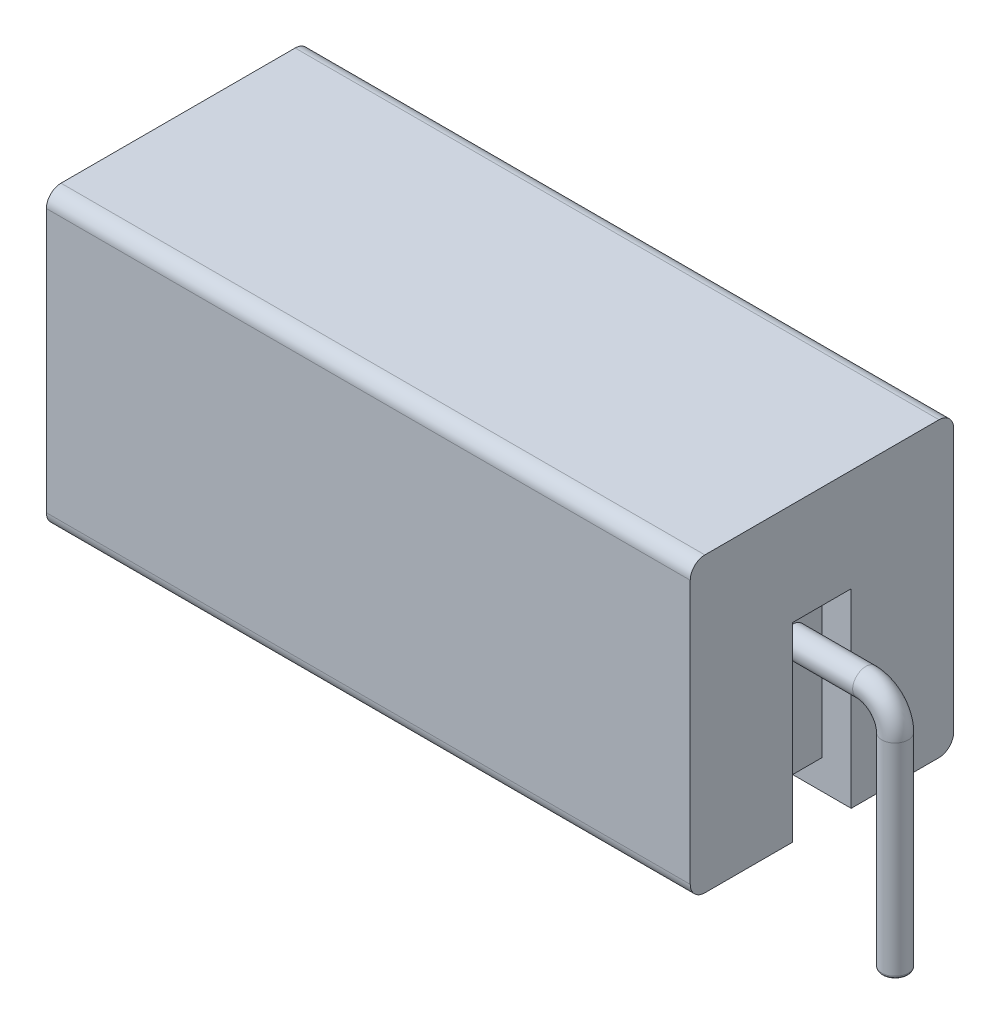
SolidWorks part; units mm, degrees
ref_plane "Front Plane" through (0, 0, 0) normal (0, 0, 1) x (1, 0, 0)
ref_plane "Top Plane" through (0, 0, 0) normal (0, 1, 0) x (1, 0, 0)
ref_plane "Right Plane" through (0, 0, 0) normal (1, 0, 0) x (0, 0, -1)
sketch "Sketch1" plane through (0, 0, 0) normal (0, 0, 1) x (1, 0, 0)
  line L1 (0, 0) -> (22, 0)
  line L2 (0, 0) -> (0, -10)
  line L3 (0, -10) -> (22, -10)
  line L4 (22, 0) -> (22, -10)
  dimension "D1" = 22
  dimension "D2" = 10
extrude "Boss-Extrude1" add sketch "Sketch1" along normal blind 9 contours L1 L4 L3 L2
fillet "Fillet2" radius 0.5 4 edges at (11, 0, 0) (11, -10, 0) (11, -10, 9) (11, 0, 9)
sketch3d "3DSketch1"
  line L1 (22, -10, 8.5) -> (22, -10, 0.5) construction
  line L3 (22, -10, 5.5) -> (22, -3.5, 5.5)
  line L4 (22, -3.5, 5.5) -> (22, -3.5, 3.5)
  line L5 (22, -3.5, 3.5) -> (22, -10, 3.5)
  line L7 (22, -10, 5.5) -> (22, -10, 3.5)
  dimension "D1" = 2
  dimension "D2" = 6.5
sketch "Sketch6" plane through (0, -10, 0) normal (0, -1, 0) x (1, 0, 0)
  line L5 (1, 5.5) -> (1, 3.5)
  line L6 (21, 5.5) -> (21, 3.5)
  line L8 (3, 8) -> (19, 8)
  line L10 (19, 1) -> (3, 1)
  line L13 (3, 8) -> (3, 5.5)
  line L14 (3, 1) -> (3, 3.5)
  line L15 (19, 8) -> (19, 5.5)
  line L16 (19, 1) -> (19, 3.5)
  line L17 (1, 5.5) -> (3, 5.5)
  line L18 (19, 5.5) -> (21, 5.5)
  line L19 (21, 3.5) -> (19, 3.5)
  line L20 (1, 3.5) -> (3, 3.5)
extrude "Cut-Extrude4" cut sketch "3DSketch1" along direction (1, 0, 0) on the side against the normal blind 1 contours L3 L4 L5 L7
sketch "Sketch8" plane through (0, 0, 0) normal (-1, 0, 0) x (0, 0, 1)
  line L0 (5.5, -10) -> (5.5, -3.5)
  line L1 (5.5, -3.5) -> (3.5, -3.5)
  line L2 (3.5, -3.5) -> (3.5, -10)
  line L3 (8.5, -10) -> (0.5, -10) construction
  line L4 (3.5, -10) -> (5.5, -10)
  dimension "D1" = 2
  dimension "D2" = 6.5
extrude "Cut-Extrude5" cut sketch "Sketch8" against normal blind 1
sketch "Sketch9" plane through (0, -10, 0) normal (0, -1, 0) x (1, 0, 0)
extrude "Cut-Extrude6" cut sketch "Sketch6" against normal blind 1
sketch "Sketch13" plane through (21, 0, 0) normal (1, 0, 0) x (0, 0, -1)
  circle A0 centre (-4.5, -5) radius 0.45
sketch3d "3DSketch4"
  line L0 (21, -5, 4.5) -> (23.5, -5, 4.5)
  line L1 (24.5, -6, 4.5) -> (24.5, -13, 4.5)
  arc A0 (24.5, -6, 4.5) -> (23.5, -5, 4.5) centre (23.5, -6, 4.5) ccw
  point P6 (24.5, -5, 4.5)
  point P7 (23.5, -6, 5.5)
  dimension "D3" = 1
  dimension "D1" = 3.5
  dimension "D2" = 8
sweep "Sweep1" add profiles "Sketch13" path "3DSketch4"
ref_plane "Plane3" through (11, 0, 0) normal (1, 0, 0) x (0, 0, -1)
mirror "Mirror1" about plane through (11, 0, 0) normal (1, 0, 0) of "Sweep1"
fillet "Fillet3" radius 0.1 2 edges at (24.5, -13, 4.05) (-2.5, -13, 4.05)
